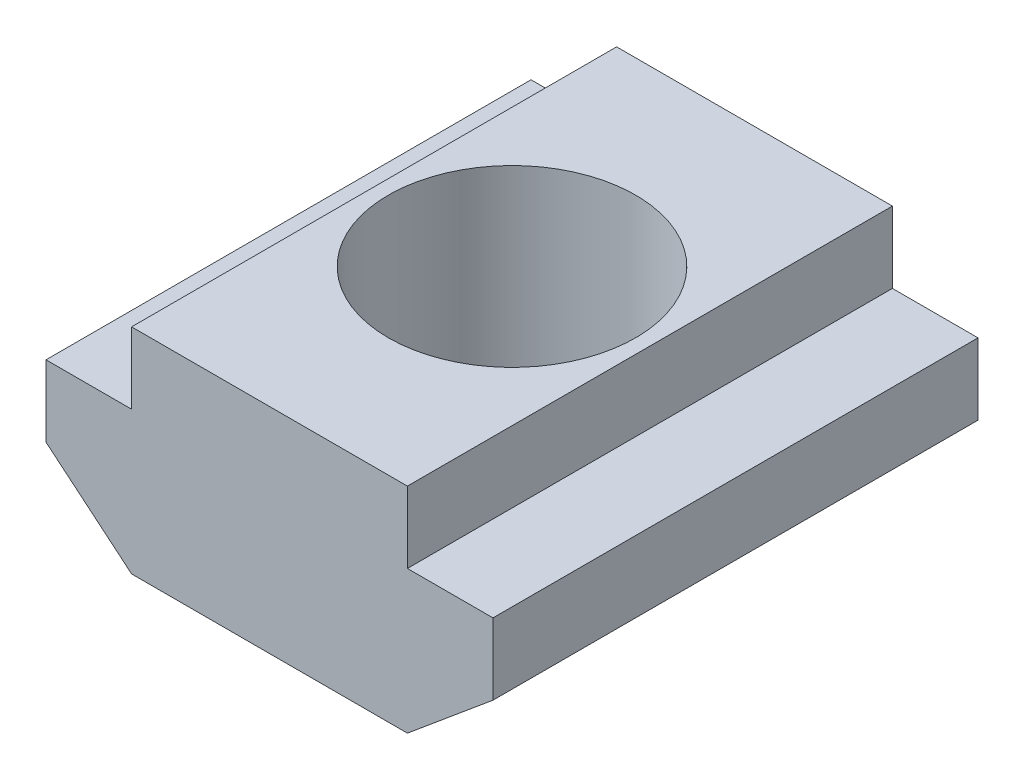
SolidWorks part; units mm, degrees
ref_plane "Top" through (0, 0, 0) normal (0, 0, 1) x (1, 0, 0)
ref_plane "Сверху" through (0, 0, 0) normal (0, 1, 0) x (1, 0, 0)
ref_plane "Справа" through (0, 0, 0) normal (1, 0, 0) x (0, 0, -1)
sketch "Эскиз1" plane through (0, 0, 0) normal (0, 0, 1) x (1, 0, 0)
  line L0 (0, 3) -> (0, 1.5)
  line L1 (0, 1.5) -> (1.8, 0)
  line L2 (1.8, 0) -> (7.6, 0)
  line L3 (7.6, 0) -> (9.4, 1.5)
  line L4 (9.4, 1.5) -> (9.4, 3)
  line L5 (9.4, 3) -> (7.6, 3)
  line L6 (7.6, 3) -> (7.6, 4.5)
  line L7 (7.6, 4.5) -> (1.8, 4.5)
  line L8 (1.8, 4.5) -> (1.8, 3)
  line L9 (1.8, 3) -> (0, 3)
extrude "Бобышка-Вытянуть1" add sketch "Эскиз1" along normal blind 10.2
hole_wizard "Сверло под метчик  спиральное M51" positions "Эскиз6" profile "Эскиз5" hole size "M5x0.8" standard "DIN" end condition through all
sketch "Эскиз6" plane through (0, 4.5, 0) normal (0, 1, 0) x (1, 0, 0)
  point P0 (4.7, -5.1)
sketch "Эскиз5" plane through (4.7, 4.5, 5.1) normal (1, 0, 0) x (0, 0, 1)
  line L0 (0, 0) -> (0, 4.5)
  line L1 (0, 4.5) -> (2.6, 4.5)
  line L2 (2.6, 4.5) -> (2.6, 0)
  line L5 (2.6, 0) -> (0, 0)
  line L11 (0, -6.35) -> (0, 107.95) construction
  dimension "Диаметр сквозного отверстия" = 5.2
  dimension "Глубина сквозного отверстия" = 4.5
